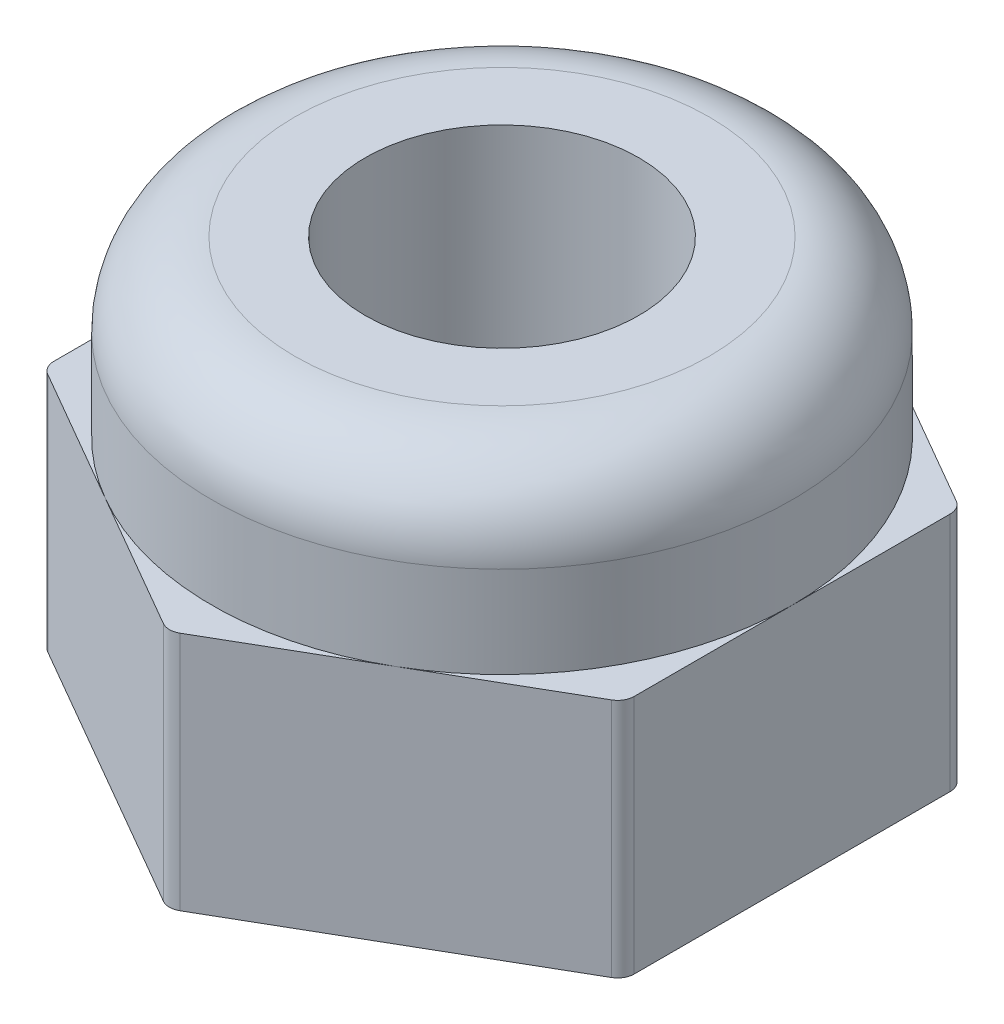
SolidWorks part; units mm, degrees
ref_plane "前视基准面" through (0, 0, 0) normal (0, 0, 1) x (1, 0, 0)
ref_plane "上视基准面" through (0, 0, 0) normal (0, 1, 0) x (1, 0, 0)
ref_plane "右视基准面" through (0, 0, 0) normal (1, 0, 0) x (0, 0, -1)
other "Configuration Table"
sketch "草图1" plane through (0, 0, 0) normal (0, 1, 0) x (1, 0, 0)
  line L1 (3.5, -2.0207) -> (3.5, 2.0207)
  line L2 (3.5, 2.0207) -> (0, 4.0415)
  line L3 (0, 4.0415) -> (-3.5, 2.0207)
  line L4 (-3.5, 2.0207) -> (-3.5, -2.0207)
  line L5 (-3.5, -2.0207) -> (0, -4.0415)
  line L6 (0, -4.0415) -> (3.5, -2.0207)
  circle A0 centre (0, 0) radius 3.5 construction
  dimension "D1" = 7
extrude "凸台-拉伸1" add sketch "草图1" along normal blind 2.9
sketch "草图2" plane through (0, 0, 0) normal (0, -1, 0) x (1, 0, 0)
  line L0 (3.5, 2.0207) -> (3.5, -2.0207) construction
  circle A0 centre (0, 0) radius 3.5
extrude "凸台-拉伸2" add sketch "草图2" against normal blind 5
fillet "圆角1" radius 1 1 edges at (0, 5, -3.5)
fillet "圆角2" radius 0.2 6 edges at (3.5, 1.45, -2.0207) (3.5, 1.45, 2.0207) (0, 1.45, 4.0415) (-3.5, 1.45, 2.0207) (-3.5, 1.45, -2.0207) (0, 1.45, -4.0415)
hole_wizard "M4 螺纹孔1" positions "草图3" profile "草图5" tap size "M4" standard "GB"
sketch "草图3" plane through (0, 0, 0) normal (0, -1, 0) x (-1, 0, 0)
  point P0 (0, 0)
sketch "草图5" plane through (0, 0, 0) normal (1, 0, 0) x (0, 0, -1)
  line L0 (0, 0) -> (0, 11.0914)
  line L1 (0, 11.0914) -> (1.65, 10.1)
  line L2 (1.65, 10.1) -> (1.65, 0.375)
  line L3 (1.65, 0.375) -> (2.025, 0)
  line L5 (2.025, 0) -> (0, 0)
  line L6 (-1.65, 0.375) -> (-2.025, 0) construction
  line L10 (0, 11.0914) -> (-1.65, 10.1) construction
  line L11 (0, -6.35) -> (0, 107.95) construction
  dimension "螺纹孔钻头直径" = 3.3
  dimension "螺纹孔钻头深度" = 10.1
  dimension "近端锥形沉头孔直径" = 4.05
  dimension "近端锥形沉头孔角度" = 90
  dimension "导头角度" = 118
cosmetic thread "孔螺蚊线1" parameters "D1"=8, "D2"=4
